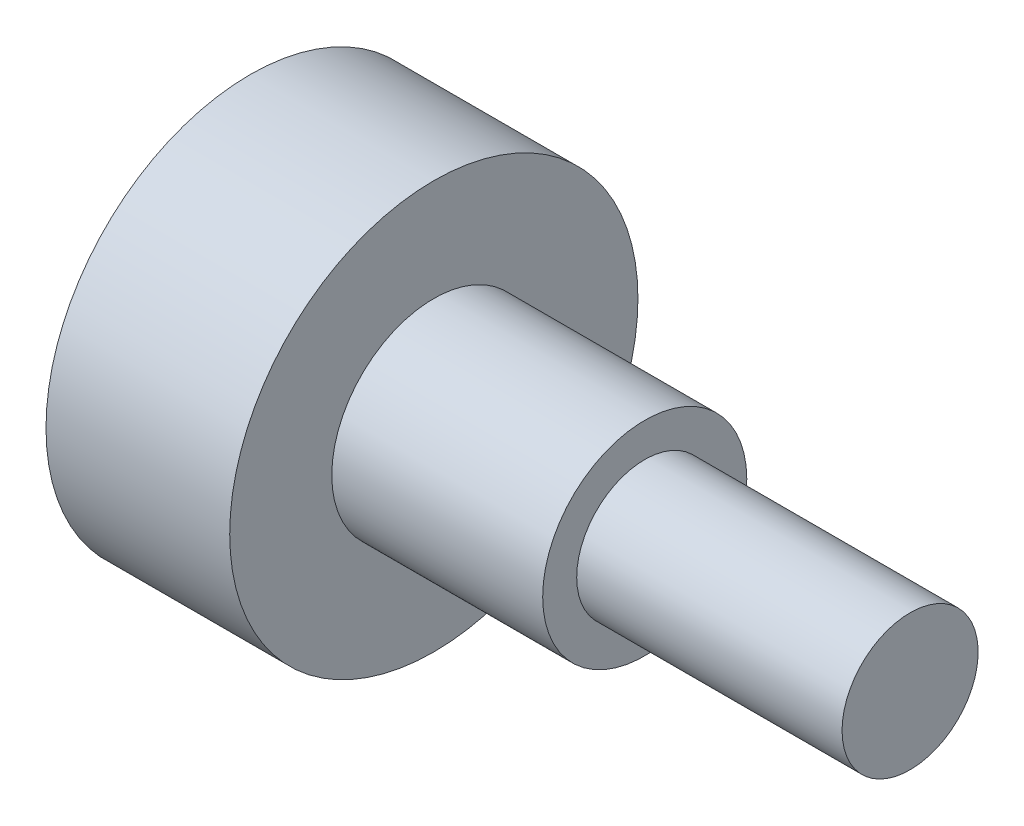
SolidWorks part; units mm, degrees
ref_plane "Ebene vorne" through (0, 0, 0) normal (0, 0, 1) x (1, 0, 0)
ref_plane "Ebene oben" through (0, 0, 0) normal (0, 1, 0) x (1, 0, 0)
ref_plane "Ebene rechts" through (0, 0, 0) normal (1, 0, 0) x (0, 0, -1)
sketch "Skizze1" plane through (0, 0, 0) normal (0, 0, 1) x (1, 0, 0)
  line L0 (-29.3044, 0) -> (48.5731, 0) construction
  line L1 (-4, 0) -> (7, 0)
  line L2 (0, 2) -> (0, 3.6)
  line L3 (0, 3.6) -> (-4, 3.6)
  line L4 (-4, 0) -> (-4, 3.6)
  line L7 (0, 2) -> (7, 2)
  line L8 (7, 0) -> (7, 2)
  dimension "D1" = 7.2
  dimension "D2" = 4
  dimension "D3" = 4
  dimension "D4" = 7
revolve "Rotation1" add sketch "Skizze1" angle 360 about L0
sketch "Skizze2" plane through (-4, 0, 0) normal (-1, 0, 0) x (0, 0, 1)
  line L1 (0, 1.7321) -> (-1.5, 0.866)
  line L2 (-1.5, 0.866) -> (-1.5, -0.866)
  line L3 (-1.5, -0.866) -> (0, -1.7321)
  line L4 (0, -1.7321) -> (1.5, -0.866)
  line L5 (1.5, -0.866) -> (1.5, 0.866)
  line L6 (1.5, 0.866) -> (0, 1.7321)
  circle A0 centre (0, 0) radius 1.5 construction
  dimension "D1" = 3
extrude "Schnitt-Linear austragen1" cut sketch "Skizze2" against normal blind 2.7
sketch "Skizze3" plane through (0, 0, 0) normal (0, 0, 1) x (1, 0, 0)
  line L0 (-0.7576, 0) -> (10.2942, 0) construction
  line L2 (0, 3.6) -> (7, 3.6)
  line L3 (0, 3.6) -> (0, 1.5)
  line L4 (0, 1.5) -> (7, 1.5)
  line L5 (0, 3.6) -> (-4, 3.6) construction
  line L6 (7, -2) -> (7, 2) construction
  line L7 (0, -3.6) -> (0, 3.6) construction
  line L9 (7, 3.6) -> (7, 1.5)
  dimension "D1" = 3
revolve "Schnitt-Rotation1" cut sketch "Skizze3" angle 360 about L0
sketch "Skizze4" plane through (0, 0, 0) normal (0, 0, 1) x (1, 0, 0)
  line L0 (0, 0) -> (10.631, 0) construction
  line L1 (7, 1.5) -> (3.1, 1.5)
  line L2 (7, 1.5) -> (7, 1)
  line L3 (7, 1) -> (3.1, 1)
  line L4 (3.1, 1.5) -> (3.1, 1)
  line L5 (0, -3.6) -> (0, 3.6) construction
  dimension "D1" = 2
  dimension "D2" = 3.1
revolve "Schnitt-Rotation2" cut sketch "Skizze4" angle 360 about L0
sketch "Skizze6" plane through (0, 0, 0) normal (0, 0, 1) x (1, 0, 0)
  line L1 (-2.7, 3) -> (0, 3)
  line L2 (-2.7, 3) -> (-2.7, 0)
  line L3 (-4, 3.6) -> (-4, -3.6) construction
  line L4 (0, 3) -> (0, 3.6)
  line L5 (-4.4056, 0) -> (6.4207, 0) construction
  line L6 (0, -3.6) -> (0, 3.6) construction
  line L7 (0, 3.6) -> (-4, 3.6) construction
  line L8 (-4, 0) -> (-2.7, 0)
  line L9 (-4, 3.6) -> (-4, 0)
  line L10 (0, 3.6) -> (-4, 3.6)
  dimension "D1" = 6
  dimension "D2" = 2.7
revolve "Schnitt-Rotation3" cut sketch "Skizze6" angle 360 about L5
